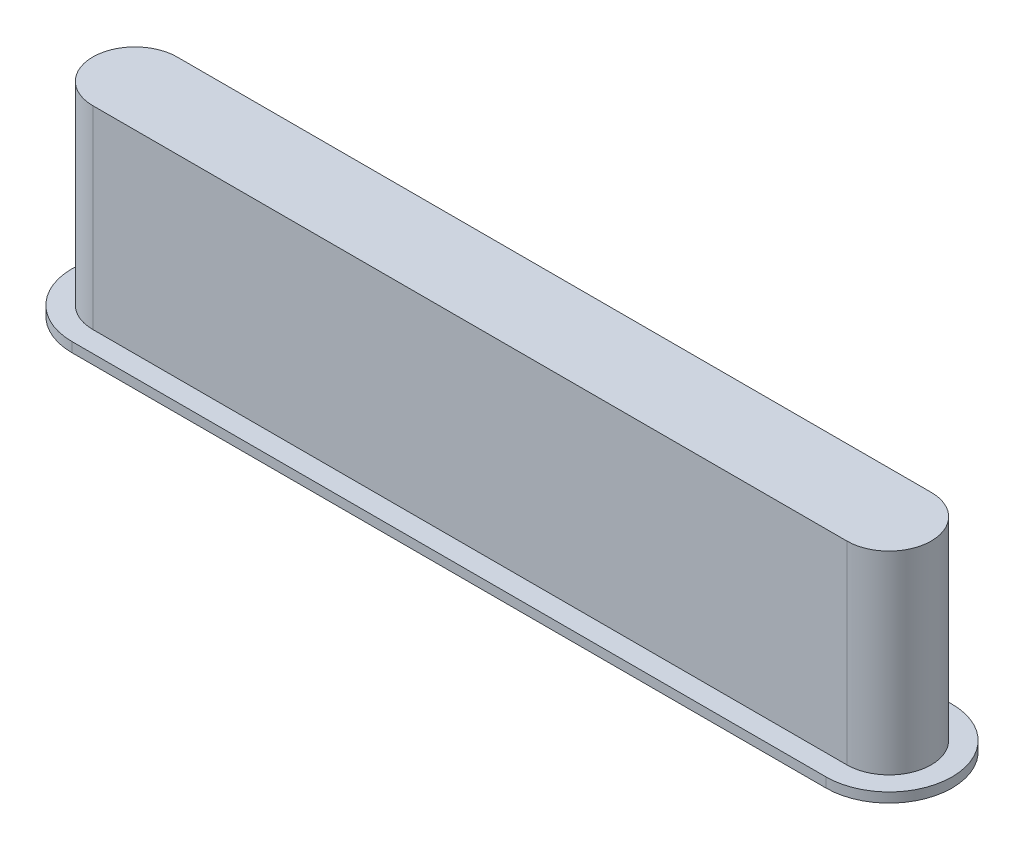
SolidWorks part; units mm, degrees
ref_plane "Front Plane" through (0, 0, 0) normal (0, 0, 1) x (1, 0, 0)
ref_plane "Top Plane" through (0, 0, 0) normal (0, 1, 0) x (1, 0, 0)
ref_plane "Right Plane" through (0, 0, 0) normal (1, 0, 0) x (0, 0, -1)
sketch "Sketch1" plane through (0, 0, 0) normal (0, 1, 0) x (1, 0, 0)
  line L0 (-9.8806, 0) -> (9.8806, 0) construction
  line L1 (-9.8806, 1.1049) -> (9.8806, 1.1049)
  line L2 (-9.8806, -1.1049) -> (9.8806, -1.1049)
  arc A0 (-9.8806, 1.1049) -> (-9.8806, -1.1049) centre (-9.8806, 0) ccw
  arc A1 (9.8806, -1.1049) -> (9.8806, 1.1049) centre (9.8806, 0) ccw
  point P2 (0, 0)
  dimension "D1" = 21.971
  dimension "D2" = 2.2098
  dimension "D3" = 19.7612
extrude "Boss-Extrude1" add sketch "Sketch1" along normal blind 5.08
sketch "Sketch3" plane through (0, 0, 0) normal (0, 1, 0) x (1, 0, 0)
  line L0 (-9.8806, 0) -> (9.8806, 0) construction
  line L1 (-9.8806, 1.651) -> (9.8806, 1.651)
  line L2 (-9.8806, -1.651) -> (9.8806, -1.651)
  arc A0 (-9.8806, 1.651) -> (-9.8806, -1.651) centre (-9.8806, 0) ccw
  arc A1 (9.8806, -1.651) -> (9.8806, 1.651) centre (9.8806, 0) ccw
  point P2 (0, 0)
  dimension "D1" = 3.302
extrude "Boss-Extrude2" add sketch "Sketch3" against normal blind 0.254
